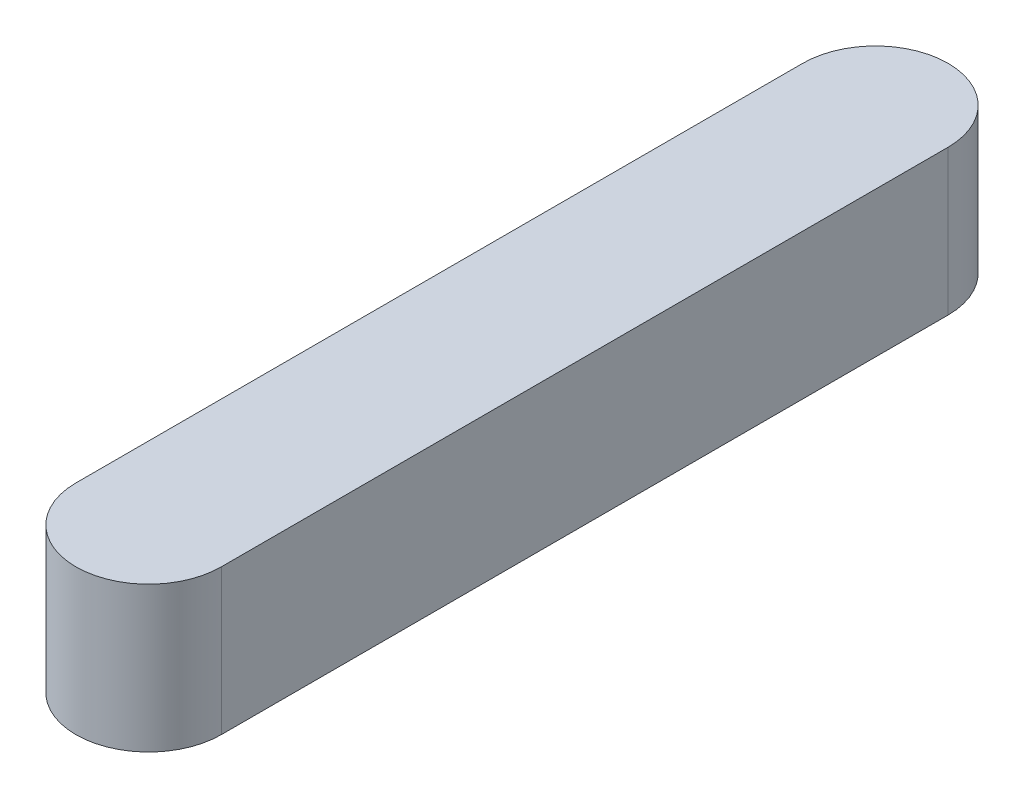
SolidWorks part; units mm, degrees
ref_plane "Plan de face" through (0, 0, 0) normal (0, 0, 1) x (1, 0, 0)
ref_plane "Plan de dessus" through (0, 0, 0) normal (0, 1, 0) x (1, 0, 0)
ref_plane "Plan de droite" through (0, 0, 0) normal (1, 0, 0) x (0, 0, -1)
sketch "Esquisse1" plane through (0, 0, 0) normal (0, 1, 0) x (1, 0, 0)
  line L0 (5, 0) -> (5, -50)
  line L1 (-5, -50) -> (-5, 0)
  arc A0 (5, -50) -> (-5, -50) centre (0, -50) cw
  arc A1 (-5, 0) -> (5, 0) centre (0, 0) cw
  point P6 (0, 0)
  dimension "D1" = 10
  dimension "D2" = 50
extrude "Boss.-Extru.1" add sketch "Esquisse1" along normal blind 10
